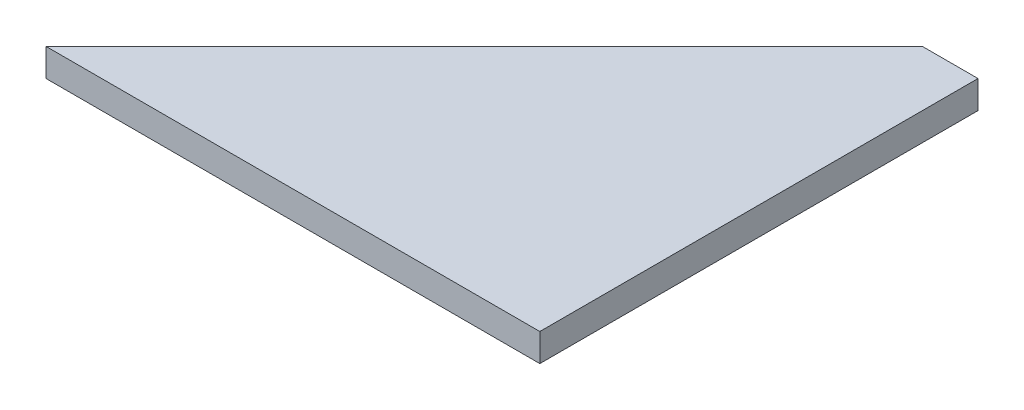
SolidWorks part; units mm, degrees
material "FiberBoard"
ref_plane "Front Plane" through (0, 0, 0) normal (0, 0, 1) x (1, 0, 0)
ref_plane "Top Plane" through (0, 0, 0) normal (0, 1, 0) x (1, 0, 0)
ref_plane "Right Plane" through (0, 0, 0) normal (1, 0, 0) x (0, 0, -1)
sketch "Sketch1" plane through (0, 0, 0) normal (0, 1, 0) x (1, 0, 0)
  line L0 (0, 0) -> (50, 50)
  line L1 (50, 50) -> (50, 0)
  line L2 (50, 0) -> (0, 0)
  dimension "D1" = 45
  dimension "D2" = 50
extrude "Boss-Extrude1" add sketch "Sketch1" along normal blind 3.175
sketch "Sketch2" plane through (50, 0, 0) normal (1, 0, 0) x (0, 0, -1)
  line L1 (0, 3.175) -> (50, 3.175)
  line L2 (0, 3.175) -> (0, 0)
  line L3 (0, 0) -> (50, 0)
  line L4 (50, 3.175) -> (50, 0)
extrude "Boss-Extrude2" add sketch "Sketch2" along normal blind 6.35
